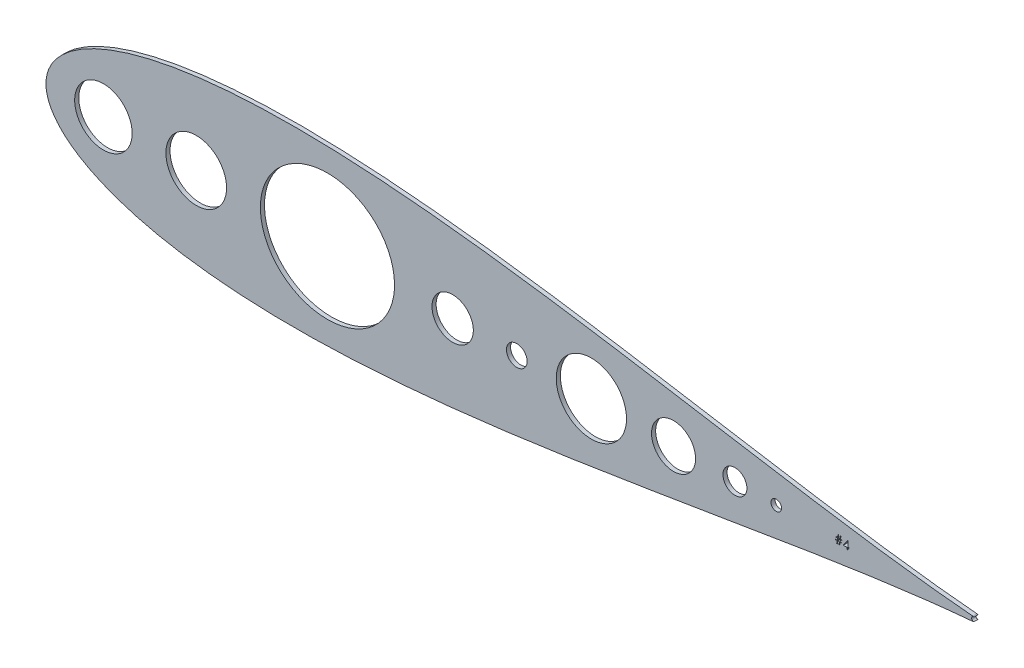
SolidWorks part; units mm, degrees
ref_plane "Front Plane" through (0, 0, 0) normal (0, 0, 1) x (1, 0, 0)
ref_plane "Top Plane" through (0, 0, 0) normal (0, 1, 0) x (1, 0, 0)
ref_plane "Right Plane" through (0, 0, 0) normal (1, 0, 0) x (0, 0, -1)
sketch "Sketch2" plane through (0, 0, 0) normal (0, 0, 1) x (1, 0, 0)
  line L0 (780.8679, 525.9414) -> (780.8679, 525.6158)
  line L1 (780.8679, 525.6158) -> (779.8971, 525.6158)
  line L2 (779.8971, 525.6158) -> (779.6336, 523.8573)
  line L3 (779.6336, 523.8573) -> (779.2397, 523.8573)
  line L4 (779.2397, 523.8573) -> (779.5033, 525.6158)
  line L5 (779.5033, 525.6158) -> (778.4643, 525.6158)
  line L6 (778.4643, 525.6158) -> (778.2007, 523.8573)
  line L7 (778.2007, 523.8573) -> (777.8069, 523.8573)
  line L8 (777.8069, 523.8573) -> (778.0705, 525.6158)
  line L9 (778.0705, 525.6158) -> (777.2208, 525.6158)
  line L10 (777.2208, 525.6158) -> (777.2208, 525.9414)
  line L11 (777.2208, 525.9414) -> (778.1193, 525.9414)
  line L12 (778.1193, 525.9414) -> (778.2954, 527.1137)
  line L13 (778.2954, 527.1137) -> (777.351, 527.1137)
  line L14 (777.351, 527.1137) -> (777.351, 527.4393)
  line L15 (777.351, 527.4393) -> (778.3442, 527.4393)
  line L16 (778.3442, 527.4393) -> (778.5884, 529.0675)
  line L17 (778.5884, 529.0675) -> (778.9813, 529.0675)
  line L18 (778.9813, 529.0675) -> (778.737, 527.4393)
  line L19 (778.737, 527.4393) -> (779.777, 527.4393)
  line L20 (779.777, 527.4393) -> (780.0213, 529.0675)
  line L21 (780.0213, 529.0675) -> (780.4141, 529.0675)
  line L22 (780.4141, 529.0675) -> (780.1698, 527.4393)
  line L23 (780.1698, 527.4393) -> (780.9982, 527.4393)
  line L24 (780.9982, 527.4393) -> (780.9982, 527.1137)
  line L25 (780.9982, 527.1137) -> (780.121, 527.1137)
  line L26 (780.121, 527.1137) -> (779.946, 525.9414)
  line L27 (779.946, 525.9414) -> (780.8679, 525.9414)
  line L28 (779.7282, 527.1137) -> (778.6882, 527.1137)
  line L29 (778.6882, 527.1137) -> (778.5131, 525.9414)
  line L30 (778.5131, 525.9414) -> (779.5521, 525.9414)
  line L31 (779.5521, 525.9414) -> (779.7282, 527.1137)
  line L32 (784.6179, 529.0675) -> (784.7105, 529.0675)
  line L33 (784.7105, 529.0675) -> (784.7105, 525.5506)
  line L34 (784.7105, 525.5506) -> (785.2967, 525.5506)
  line L35 (785.2967, 525.5506) -> (785.2967, 525.0296)
  line L36 (785.2967, 525.0296) -> (784.7105, 525.0296)
  line L37 (784.7105, 525.0296) -> (784.7105, 523.8573)
  line L38 (784.7105, 523.8573) -> (784.2546, 523.8573)
  line L39 (784.2546, 523.8573) -> (784.2546, 525.0296)
  line L40 (784.2546, 525.0296) -> (781.8449, 525.0296)
  line L41 (781.8449, 525.0296) -> (784.6179, 529.0675)
  line L42 (784.2546, 525.5506) -> (784.2546, 527.7568)
  line L43 (784.2546, 527.7568) -> (782.7404, 525.5506)
  line L44 (782.7404, 525.5506) -> (784.2546, 525.5506)
  circle A0 centre (327.5065, 525.6884) radius 17.6573
  arc A1 (862.0578, 526.9234) -> (862.0578, 524.4535) centre (861.9033, 525.6884) ccw
  circle A2 centre (740.7017, 525.6884) radius 3.255
  circle A3 centre (715.3261, 525.6884) radius 7.3636
  circle A4 centre (677.6347, 525.6884) radius 13.5351
  circle A5 centre (627.1597, 525.6884) radius 21.5742
  circle A6 centre (581.3547, 525.6884) radius 6.35
  circle A7 centre (541.9847, 525.6884) radius 12.7
  circle A8 centre (384.5047, 525.6884) radius 18.6309
  arc A9 (862.0578, 526.9234) -> (861.5012, 527.0901) centre (861.3847, 525.6884) ccw
  arc A10 (861.5012, 524.2868) -> (862.0578, 524.4535) centre (861.3847, 525.6884) ccw
  ellipse E0 centre (465.0779, 525.6884) end of major axis (506.2725, 525.6884) minor radius 38.9432
  spline S0 degree 3 poles (861.5012, 527.0901) (861.0428, 527.1282) (857.5877, 527.4193) (850.7833, 528.0482) (840.6831, 529.0989) (829.4849, 530.3882) (817.2305, 531.9238) (803.9773, 533.7073) (789.7826, 535.7347) (774.7077, 537.9956) (758.8168, 540.4738) (742.1763, 543.1472) (724.8551, 545.9882) (706.9239, 548.964) (688.4553, 552.0372) (669.5234, 555.1659) (650.2039, 558.305) (630.574, 561.406) (610.7123, 564.4186) (590.6986, 567.291) (570.6145, 569.9706) (550.5426, 572.4052) (530.5674, 574.5435) (510.7743, 576.3363) (491.2507, 577.7367) (472.085, 578.7015) (453.3674, 579.1918) (435.189, 579.1736) (417.6429, 578.618) (400.8231, 577.5033) (384.8257, 575.8133) (369.7483, 573.5404) (355.6917, 570.6837) (342.7596, 567.2529) (331.0615, 563.2681) (320.7141, 558.7648) (311.843, 553.8025) (304.5807, 548.482) (299.0496, 542.9771) (295.305, 537.5789) (293.2168, 532.7086) (292.3736, 528.8017) (292.1816, 525.6884) (292.3736, 522.5752) (293.2168, 518.6683) (295.305, 513.798) (299.0496, 508.3997) (304.5807, 502.8948) (311.843, 497.5744) (320.7141, 492.6121) (331.0615, 488.1087) (342.7596, 484.1239) (355.6917, 480.6931) (369.7483, 477.8365) (384.8257, 475.5636) (400.8231, 473.8736) (417.6429, 472.7589) (435.189, 472.2033) (453.3674, 472.1851) (472.085, 472.6754) (491.2507, 473.6402) (510.7743, 475.0406) (530.5674, 476.8333) (550.5426, 478.9717) (570.6145, 481.4063) (590.6986, 484.0859) (610.7123, 486.9583) (630.574, 489.9709) (650.2039, 493.0719) (669.5234, 496.2109) (688.4553, 499.3397) (706.9239, 502.4128) (724.8551, 505.3887) (742.1763, 508.2297) (758.8168, 510.9031) (774.7077, 513.3813) (789.7826, 515.6422) (803.9773, 517.6696) (817.2305, 519.4531) (829.4849, 520.9887) (840.6831, 522.278) (850.7833, 523.3287) (857.5877, 523.9576) (861.0428, 524.2486) (861.5012, 524.2868) knots 0.020157 0.020157 0.020157 0.020157 0.021271 0.028553 0.036781 0.04592 0.055932 0.066773 0.078397 0.090755 0.103793 0.117456 0.131686 0.146422 0.1616 0.177156 0.193024 0.209135 0.225421 0.241812 0.258238 0.274629 0.290914 0.307025 0.322893 0.338448 0.353626 0.368361 0.38259 0.396253 0.40929 0.421647 0.43327 0.444109 0.454119 0.463255 0.471479 0.478755 0.485052 0.490344 0.49461 0.497833 0.5 0.502167 0.50539 0.509656 0.514948 0.521245 0.528521 0.536745 0.545881 0.555891 0.56673 0.578353 0.59071 0.603747 0.61741 0.631639 0.646374 0.661552 0.677107 0.692975 0.709086 0.725371 0.741762 0.758188 0.774579 0.790865 0.806976 0.822844 0.8384 0.853578 0.868314 0.882544 0.896207 0.909245 0.921603 0.933227 0.944068 0.95408 0.963219 0.971447 0.978729 0.979843 0.979843 0.979843 0.979843
extrude "Boss-Extrude1" add sketch "Sketch2" along normal blind 2.54 contours A9 S0 A10 A1 L40 L41 L32 L33 L34 L35 L36 L37 L38 L39 L26 L27 L0 L1 L2 L3 L4 L5 L6 L7 L8 L9 L10 L11 L12 L13 L14 L15 L16 L17 L18 L19 L20 L21 L22 L23 L24 L25 A0 A2 A3
